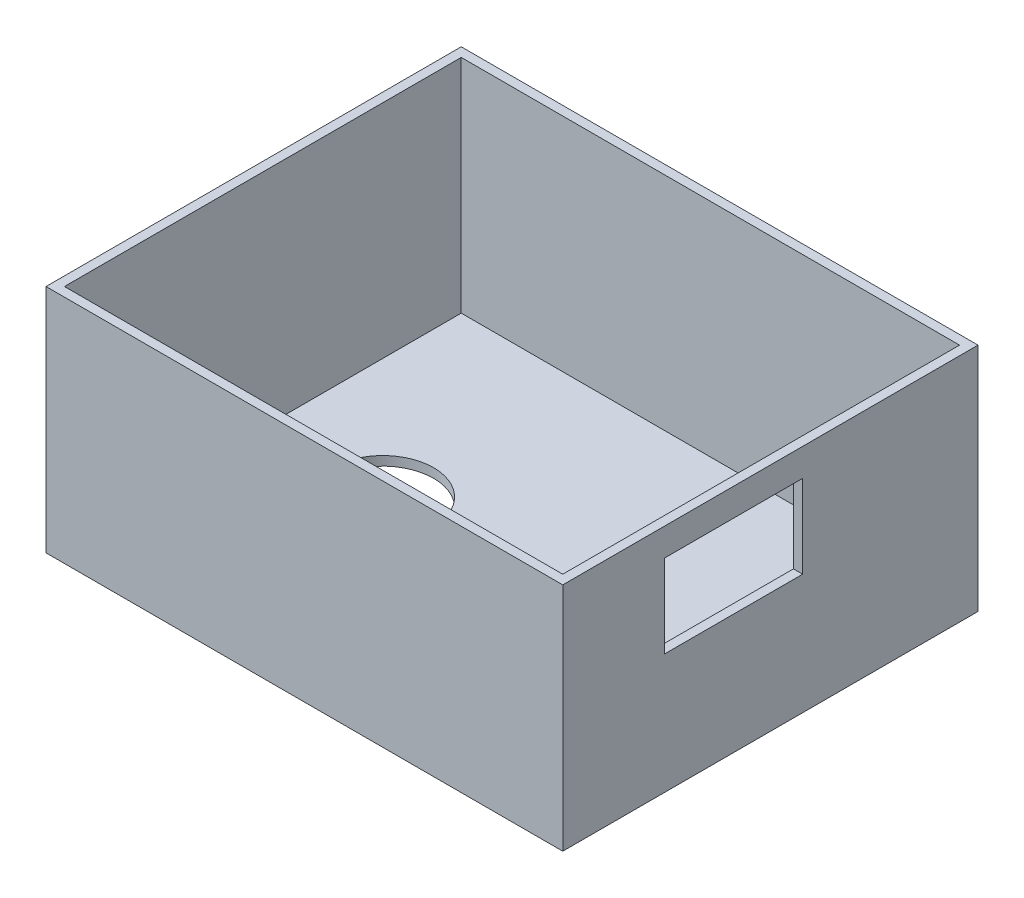
SolidWorks part; units mm, degrees
ref_plane "Front Plane" through (0, 0, 0) normal (0, 0, 1) x (1, 0, 0)
ref_plane "Top Plane" through (0, 0, 0) normal (0, 1, 0) x (1, 0, 0)
ref_plane "Right Plane" through (0, 0, 0) normal (1, 0, 0) x (0, 0, -1)
sketch "Sketch1" plane through (0, 0, 0) normal (0, 1, 0) x (1, 0, 0)
  line L1 (-28, 22.5) -> (28, 22.5)
  line L2 (-28, 22.5) -> (-28, -22.5)
  line L3 (-28, -22.5) -> (28, -22.5)
  line L4 (28, 22.5) -> (28, -22.5)
  line L5 (0, -22.5) -> (0, 22.5) construction
  line L6 (-28, 0) -> (28, 0) construction
  point P0 (0, 0)
  dimension "D1" = 56
  dimension "D2" = 45
extrude "Boss-Extrude1" add sketch "Sketch1" along normal blind 25
sketch "Sketch2" plane through (0, 0, 0) normal (0, -1, 0) x (1, 0, 0)
  line L0 (-28, -22.5) -> (-28, 22.5) construction
  circle A0 centre (-14, 0) radius 5.5
  point P4 (-13, 0)
  dimension "D1" = 11
  dimension "D2" = 14
extrude "Cut-Extrude1" cut sketch "Sketch2" against normal blind 15
sketch "Sketch3" plane through (0, 25, 0) normal (0, 1, 0) x (1, 0, 0)
  line L1 (-27, 21.5) -> (27, 21.5)
  line L2 (-27, 21.5) -> (-27, -21.5)
  line L3 (-27, -21.5) -> (27, -21.5)
  line L4 (27, 21.5) -> (27, -21.5)
  line L5 (0, -21.5) -> (0, 21.5) construction
  line L6 (-27, 0) -> (27, 0) construction
  point P0 (0, 0)
  dimension "D1" = 54
  dimension "D2" = 43
extrude "Cut-Extrude2" cut sketch "Sketch3" against normal blind 24
sketch "Sketch4" plane through (28, 0, 0) normal (1, 0, 0) x (0, 0, -1)
  line L1 (-11.5, 22) -> (3.5, 22)
  line L2 (-11.5, 22) -> (-11.5, 13)
  line L3 (-11.5, 13) -> (3.5, 13)
  line L4 (3.5, 22) -> (3.5, 13)
  line L5 (-4, 13) -> (-4, 22) construction
  line L6 (-11.5, 17.5) -> (3.5, 17.5) construction
  line L7 (-22.5, 25) -> (22.5, 25) construction
  line L8 (-22.5, 25) -> (-22.5, 0) construction
  point P0 (-4, 17.5)
  dimension "D1" = 3
  dimension "D2" = 12
  dimension "D3" = 15
  dimension "D4" = 11
extrude "Cut-Extrude3" cut sketch "Sketch4" against normal blind 24
